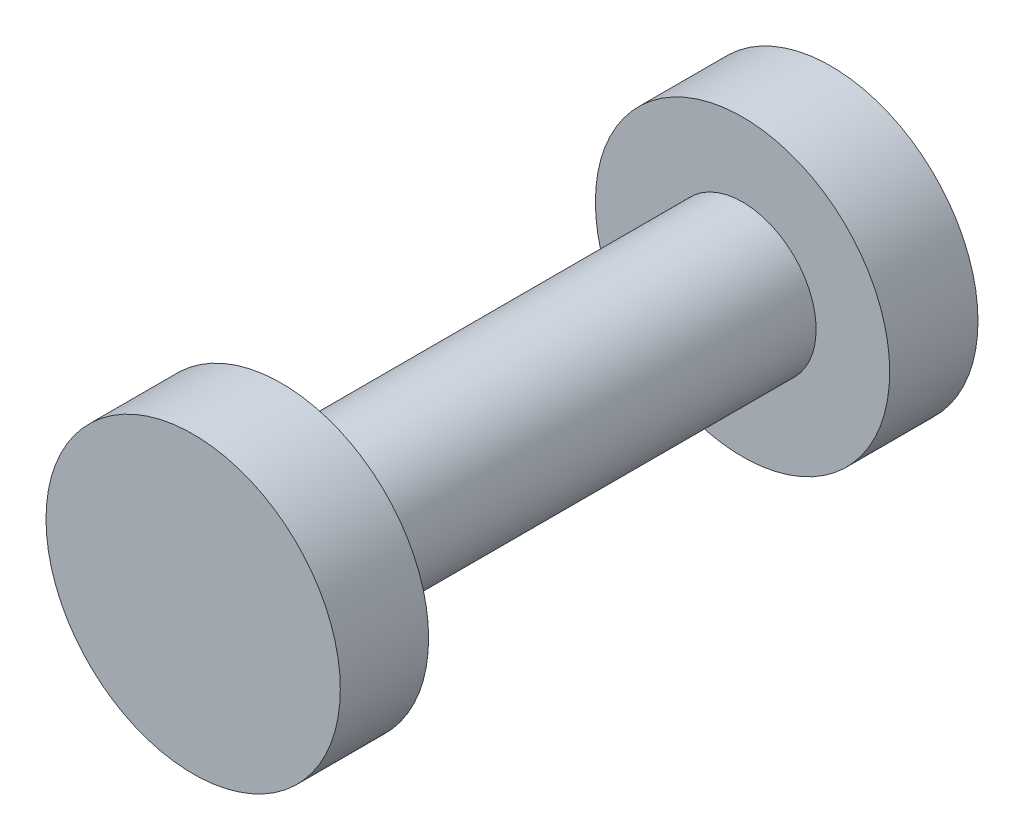
SolidWorks part; units mm, degrees
ref_plane "Front Plane" through (0, 0, 0) normal (0, 0, 1) x (1, 0, 0)
ref_plane "Top Plane" through (0, 0, 0) normal (0, 1, 0) x (1, 0, 0)
ref_plane "Right Plane" through (0, 0, 0) normal (1, 0, 0) x (0, 0, -1)
sketch "Sketch1" plane through (0, 0, 0) normal (0, 0, 1) x (1, 0, 0)
  circle A0 centre (0, 0) radius 1.5
  dimension "D1" = 3
extrude "Boss-Extrude1" add sketch "Sketch1" along normal mid plane 13
sketch "Sketch2" plane through (0, 0, 6.5) normal (0, 0, 1) x (1, 0, 0)
  circle A0 centre (0, 0) radius 3
  dimension "D1" = 6
extrude "Boss-Extrude2" add sketch "Sketch2" against normal blind 1.8
mirror "Mirror1" about plane through (0, 0, 0) normal (0, 0, 1) of "Boss-Extrude2"
